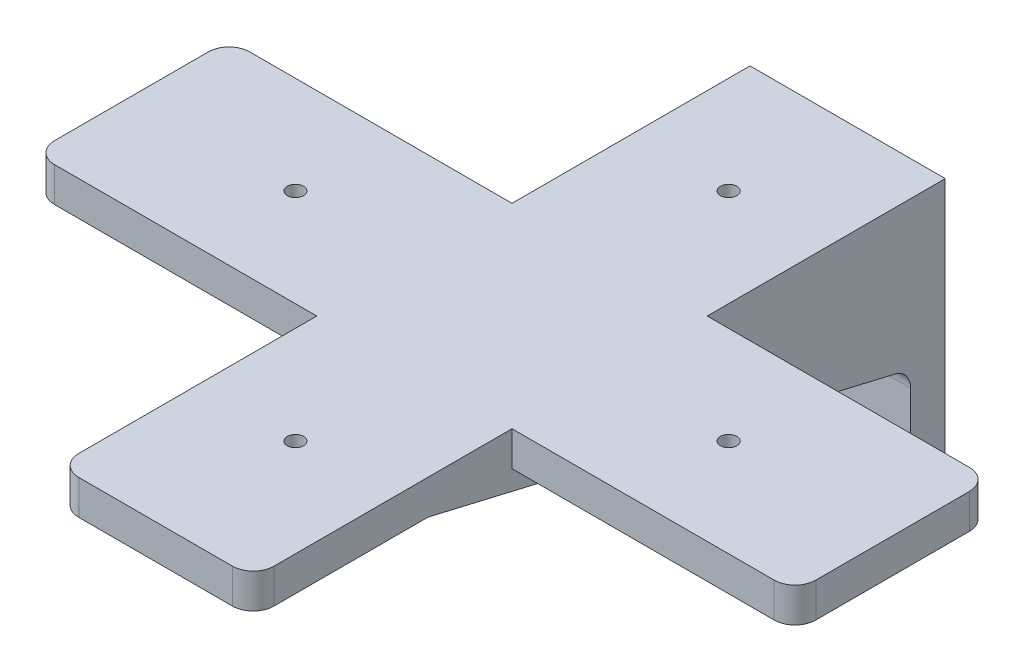
SolidWorks part; units mm, degrees
ref_plane "Front Plane" through (0, 0, 0) normal (0, 0, 1) x (1, 0, 0)
ref_plane "Top Plane" through (0, 0, 0) normal (0, 1, 0) x (1, 0, 0)
ref_plane "Right Plane" through (0, 0, 0) normal (1, 0, 0) x (0, 0, -1)
sketch "Sketch1" plane through (0, 0, 0) normal (0, 0, 1) x (1, 0, 0)
  line L1 (-17.9134, -27.1209) -> (17.9134, -27.1209)
  line L2 (-17.9134, -27.1209) -> (-17.9134, 27.1208)
  line L3 (-17.9134, 27.1208) -> (17.9134, 27.1208)
  line L4 (17.9134, -27.1209) -> (17.9134, 27.1208)
  line L5 (-17.9134, -27.1209) -> (17.9134, 27.1208) construction
  line L6 (-17.9134, 27.1208) -> (17.9134, -27.1209) construction
  point P0 (0, 0)
  dimension "D1" = 35.8267
  dimension "D2" = 54.2417
extrude "Boss-Extrude1" add sketch "Sketch1" along normal blind 6.35
sketch "Sketch2" plane through (0, 27.1208, 0) normal (0, 1, 0) x (1, 0, 0)
  line L0 (17.9134, 0) -> (-17.9134, 0) construction
  line L1 (-17.9133, -127) -> (17.9134, -127)
  line L2 (-17.9133, -127) -> (-17.9133, 0)
  line L3 (-17.9133, 0) -> (17.9134, 0)
  line L4 (17.9134, -127) -> (17.9134, 0)
  dimension "D1" = 127
  dimension "D2" = 35.8267
extrude "Boss-Extrude2" add sketch "Sketch2" against normal blind 6.35
sketch "Sketch4" plane through (17.9134, 0, 0) normal (1, 0, 0) x (0, 0, -1)
  line L0 (-6.35, 0) -> (-94.9064, 20.7708)
  line L1 (-6.35, -27.1209) -> (-6.35, 20.7708) construction
  line L2 (-127, 20.7708) -> (-6.35, 20.7708) construction
  line L3 (-94.9064, 20.7708) -> (-6.35, 20.7708)
  line L4 (-6.35, 20.7708) -> (-6.35, 0)
ref_plane "Plane1" through (0, 0, 0) normal (1, 0, 0) x (0, 0, -1)
extrude "Boss-Extrude3" add sketch "Sketch4" against normal blind 5.08
mirror "Mirror1" about plane through (0, 0, 0) normal (1, 0, 0) of "Boss-Extrude3"
fillet "Fillet1" radius 3.81 8 edges at (17.9134, 23.9458, 127) (-17.9133, 23.9458, 127) (15.3734, 20.7708, 94.9064) (-15.3733, 20.7708, 94.9064) (15.3734, 0, 6.35) (-15.3734, 0, 6.35) (-17.9134, -27.1209, 3.175) (17.9134, -27.1209, 3.175)
sketch "Sketch5" plane through (0, 0, 6.35) normal (0, 0, 1) x (1, 0, 0)
  line L0 (17.8837, -27.1209) -> (17.9134, -12.3889) construction
  line L1 (17.9134, -23.3109) -> (17.9134, -3.0198) construction
  line L2 (17.9134, -12.3889) -> (-17.9134, -12.3889) construction
  line L3 (-14.1034, -27.1209) -> (30.5893, -27.1209) construction
  line L4 (-9.906, -12.3889) -> (9.906, -12.3889) construction
  line L5 (-9.906, -12.3889) -> (-9.906, 7.4231) construction
  line L6 (-9.906, 7.4231) -> (9.906, 7.4231) construction
  line L7 (9.906, -12.3889) -> (9.906, 7.4231) construction
  line L8 (-17.9134, -3.0198) -> (-17.9134, -23.3109) construction
  line L9 (0, 7.4231) -> (0, -15.5639) construction
  line L10 (0, -15.5639) -> (-9.906, -2.4829) construction
  line L11 (-9.906, -2.4829) -> (9.906, -2.4829) construction
  circle A0 centre (-9.906, 7.4231) radius 1.4986
  circle A1 centre (9.906, 7.4231) radius 1.4986
  circle A2 centre (9.906, -12.3889) radius 1.4986
  circle A3 centre (-9.906, -12.3889) radius 1.4986
  point P18 (0, -4.0704)
  point P29 (0, -2.4829)
  dimension "D4" = 2.9972
  dimension "D1" = 14.732
  dimension "D2" = 19.812
  dimension "D3" = 8.0074
  dimension "D5" = 4
extrude "Cut-Extrude1" [suppressed] cut sketch "Sketch5" against normal blind 6.35
sketch "Sketch6" plane through (0, 27.1208, 0) normal (0, 1, 0) x (1, 0, 0)
  line L0 (0, 0) -> (0, -135.9417) construction
  line L1 (0, -69.0334) -> (0, 69.0334) construction
  line L2 (-17.9134, -61.595) -> (17.9134, -61.595) construction
  line L3 (-17.9134, -123.19) -> (-17.9134, 0) construction
  line L4 (17.9134, -123.19) -> (17.9134, 0) construction
  line L6 (-66.04, -79.5084) -> (66.04, -79.5084)
  line L7 (-69.85, -75.6983) -> (-69.85, -47.4916)
  line L8 (-66.04, -43.6817) -> (66.04, -43.6817)
  line L9 (69.85, -75.6983) -> (69.85, -47.4916)
  line L10 (-69.85, -79.5084) -> (69.85, -43.6817) construction
  line L11 (-69.85, -43.6817) -> (69.85, -79.5084) construction
  arc A0 (66.04, -79.5084) -> (69.85, -75.6983) centre (66.04, -75.6983) ccw
  arc A1 (66.04, -43.6817) -> (69.85, -47.4916) centre (66.04, -47.4916) cw
  arc A2 (-66.04, -79.5084) -> (-69.85, -75.6983) centre (-66.04, -75.6983) cw
  arc A3 (-69.85, -47.4916) -> (-66.04, -43.6817) centre (-66.04, -47.4916) cw
  point P11 (0, -61.595)
  point P12 (0, -61.595)
  dimension "D3" = 3.81
  dimension "D1" = 35.8267
  dimension "D2" = 139.7
extrude "Boss-Extrude4" add sketch "Sketch6" against normal blind 6.35
sketch "Sketch7" plane through (0, 27.1208, 0) normal (0, 1, 0) x (1, 0, 0)
  line L0 (-17.9134, -21.8408) -> (17.9134, -21.8408) construction
  line L1 (-17.9134, -43.6817) -> (-17.9134, 0) construction
  line L2 (17.9134, -43.6817) -> (17.9134, 0) construction
  line L3 (17.9134, -21.8408) -> (41.9767, -43.6817) construction
  line L4 (66.04, -43.6817) -> (17.9134, -43.6817) construction
  line L5 (41.9767, -43.6817) -> (41.9767, -79.5084) construction
  line L6 (17.9133, -79.5084) -> (66.04, -79.5084) construction
  line L7 (41.9767, -79.5084) -> (17.9133, -101.3492) construction
  line L8 (17.9134, -123.19) -> (17.9133, -79.5084) construction
  line L9 (17.9133, -101.3492) -> (-17.9134, -101.3492) construction
  line L10 (-17.9134, -123.19) -> (-17.9134, -79.5084) construction
  line L11 (-17.9134, -101.3492) -> (-41.9767, -79.5084) construction
  line L12 (-66.04, -79.5084) -> (-17.9134, -79.5084) construction
  line L13 (-41.9767, -79.5084) -> (-41.9767, -43.6817) construction
  line L14 (-17.9134, -43.6817) -> (-66.04, -43.6817) construction
  line L15 (-41.9767, -43.6817) -> (-17.9134, -21.8408) construction
  line L16 (0, -21.8408) -> (0, -101.3492) construction
  line L17 (0, -101.3492) -> (-41.9767, -61.595) construction
  line L18 (-41.9767, -61.595) -> (41.9767, -61.595) construction
  circle A0 centre (0, -21.8408) radius 1.4986
  circle A1 centre (39.7542, -61.595) radius 1.4986
  circle A2 centre (0, -101.3492) radius 1.4986
  circle A3 centre (-39.7542, -61.595) radius 1.4986
  point P30 (0, -61.595)
  point P39 (0, -61.595)
  dimension "D1" = 2.9972
  dimension "D2" = 4
extrude "Cut-Extrude2" cut sketch "Sketch7" against normal blind 6.35
